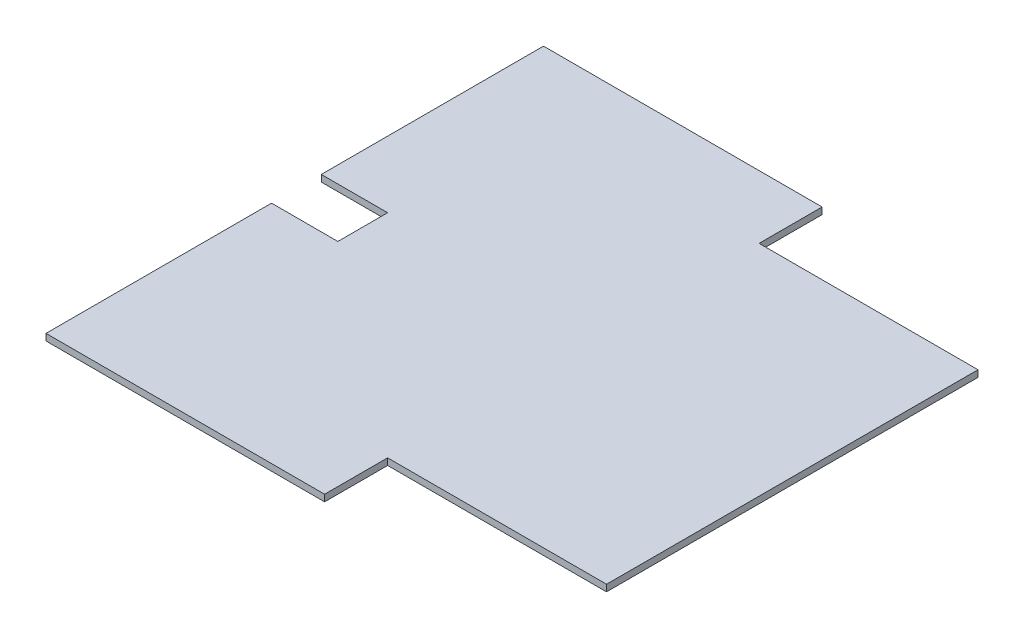
SolidWorks part; units mm, degrees
ref_plane "Front Plane" through (0, 0, 0) normal (0, 0, 1) x (1, 0, 0)
ref_plane "Top Plane" through (0, 0, 0) normal (0, 1, 0) x (1, 0, 0)
ref_plane "Right Plane" through (0, 0, 0) normal (1, 0, 0) x (0, 0, -1)
sketch "Sketch1" plane through (0, 0, 0) normal (0, 1, 0) x (1, 0, 0)
  line L1 (-75, 75) -> (75, 75)
  line L2 (-75, 75) -> (-75, -75)
  line L3 (-75, -75) -> (75, -75)
  line L4 (75, 75) -> (75, -75)
  line L5 (-75, 75) -> (75, -75) construction
  line L6 (-75, -75) -> (75, 75) construction
  point P0 (0, 0)
  dimension "D1" = 150
  dimension "D2" = 150
extrude "Boss-Extrude1" add sketch "Sketch1" along normal blind 2
sketch "Sketch2" plane through (0, 2, 0) normal (0, 1, 0) x (1, 0, 0)
  line L0 (75, -75) -> (75, 75) construction
  line L1 (-75, -75) -> (75, -75) construction
  point P0 (55, -50)
  dimension "D1" = 20
  dimension "D2" = 25
sketch "Sketch3" plane through (0, 2, 0) normal (0, 1, 0) x (1, 0, 0)
  line L0 (-75, -75) -> (75, -75) construction
  line L1 (-75, 75) -> (-75, -75) construction
  line L2 (75, 75) -> (-75, 75) construction
  line L3 (75, -75) -> (75, 75) construction
  point P0 (-55, -50)
  point P1 (-55, 50)
  point P2 (55, 50)
  dimension "D1" = 25
  dimension "D2" = 20
  dimension "D3" = 20
  dimension "D4" = 25
  dimension "D5" = 20
  dimension "D6" = 25
sketch "Sketch4" plane through (0, 2, 0) normal (0, 1, 0) x (1, 0, 0)
  line L0 (-75, 75) -> (-75, -75) construction
  line L1 (-75, 8) -> (-55, 8)
  line L2 (-75, 8) -> (-75, -7)
  line L3 (-75, -7) -> (-55, -7)
  line L4 (-55, 8) -> (-55, -7)
  line L5 (75, 75) -> (-75, 75) construction
  point P6 (-65, -7)
  dimension "D1" = 20
  dimension "D2" = 15
  dimension "D3" = 67
extrude "Cut-Extrude2" cut sketch "Sketch4" against normal up to next
sketch "Sketch7" plane through (0, 0, 0) normal (0, -1, 0) x (1, 0, 0)
  line L0 (55, 75) -> (55, -67.6889) construction
  line L1 (-75, 75) -> (75, 75) construction
  line L3 (75, 75) -> (9, 75)
  line L4 (75, 75) -> (75, 56)
  line L5 (75, 56) -> (9, 56)
  line L6 (9, 75) -> (9, 56)
  line L7 (75, -75) -> (9, -75)
  line L8 (75, -75) -> (75, -56)
  line L9 (75, -56) -> (9, -56)
  line L10 (9, -75) -> (9, -56)
  dimension "D1" = 19
  dimension "D2" = 66
  dimension "D3" = 66
  dimension "D4" = 19
extrude "Cut-Extrude3" cut sketch "Sketch7" against normal up to next
sketch "Sketch9" plane through (0, 0, 0) normal (0, -1, 0) x (1, 0, 0)
  line L0 (-65, 75) -> (-65, -75) construction
  line L1 (-75, 75) -> (9, 75) construction
  line L2 (9, -75) -> (-75, -75) construction
  line L3 (-75, 7) -> (-75, 75) construction
  dimension "D1" = 10
